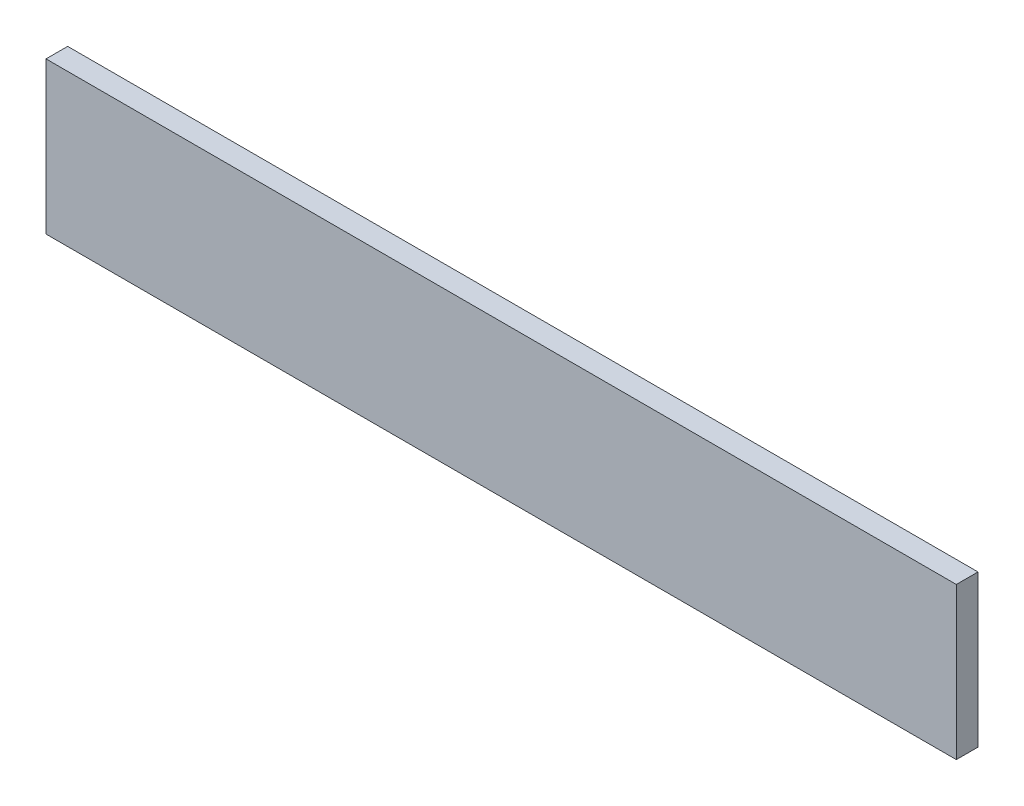
SolidWorks part; units mm, degrees
material "Cedar"
ref_plane "Front Plane" through (0, 0, 0) normal (0, 0, 1) x (1, 0, 0)
ref_plane "Top Plane" through (0, 0, 0) normal (0, 1, 0) x (1, 0, 0)
ref_plane "Right Plane" through (0, 0, 0) normal (1, 0, 0) x (0, 0, -1)
sketch "Sketch1" plane through (0, 0, 0) normal (0, 0, 1) x (1, 0, 0)
  line L1 (-191.8705, 43.6186) -> (341.5295, 43.6186)
  line L2 (-191.8705, 43.6186) -> (-191.8705, -45.2814)
  line L3 (-191.8705, -45.2814) -> (341.5295, -45.2814)
  line L4 (341.5295, 43.6186) -> (341.5295, -45.2814)
  dimension "D1" = 533.4
  dimension "D2" = 88.9
extrude "Boss-Extrude1" add sketch "Sketch1" along normal blind 12.7
